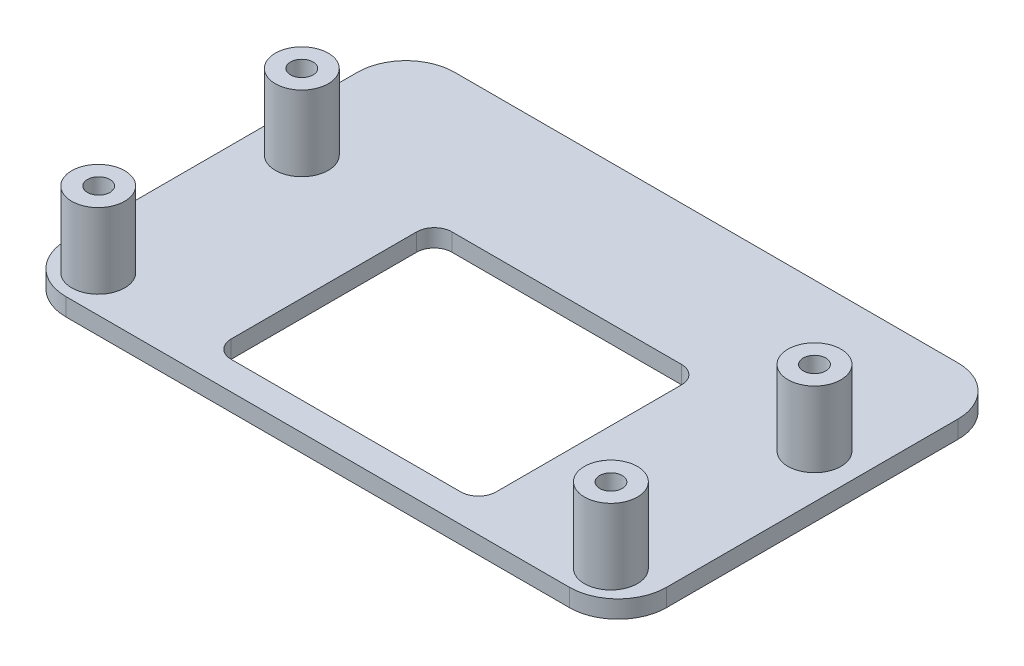
SolidWorks part; units mm, degrees
ref_plane "前视基准面" through (0, 0, 0) normal (0, 0, 1) x (1, 0, 0)
ref_plane "上视基准面" through (0, 0, 0) normal (0, 1, 0) x (1, 0, 0)
ref_plane "右视基准面" through (0, 0, 0) normal (1, 0, 0) x (0, 0, -1)
other "Configuration Table"
sketch "草图1" plane through (0, 0, 0) normal (0, 1, 0) x (1, 0, 0)
  line L1 (-34.4994, 19.3243) -> (33.5006, 19.3243)
  line L2 (-34.4994, 19.3243) -> (-34.4994, -24.6757)
  line L3 (-34.4994, -24.6757) -> (33.5006, -24.6757)
  line L4 (33.5006, 19.3243) -> (33.5006, -24.6757)
  dimension "D1" = 68
  dimension "D2" = 44
extrude "凸台-拉伸1" add sketch "草图1" along normal blind 2
fillet "圆角1" radius 5.5 4 edges at (33.5006, 1, -19.3243) (33.5006, 1, 24.6757) (-34.4994, 1, 24.6757) (-34.4994, 1, -19.3243)
sketch "草图2" plane through (0, 0, 0) normal (0, -1, 0) x (1, 0, 0)
  line L0 (-28.9994, 24.6757) -> (28.0006, 24.6757) construction
  line L1 (-15.4994, 21.4757) -> (14.5006, 21.4757)
  line L2 (-15.4994, 21.4757) -> (-15.4994, -3.5243)
  line L3 (-15.4994, -3.5243) -> (14.5006, -3.5243)
  line L4 (14.5006, 21.4757) -> (14.5006, -3.5243)
  line L5 (-15.4994, 21.4757) -> (14.5006, -3.5243) construction
  line L6 (-15.4994, -3.5243) -> (14.5006, 21.4757) construction
  point P0 (-0.4994, 8.9757)
  point P5 (0, 0)
  point P8 (-0.4994, 24.6757)
  dimension "D1" = 15.7
  dimension "D2" = 30
  dimension "D3" = 25
extrude "切除-拉伸1" cut sketch "草图2" against normal through all
fillet "圆角2" radius 2 4 edges at (-15.4994, 1, -3.5243) (-15.4994, 1, 21.4757) (14.5006, 1, 21.4757) (14.5006, 1, -3.5243)
sketch "草图3" plane through (0, 2, 0) normal (0, 1, 0) x (1, 0, 0)
  circle A0 centre (-29.5244, 2.5493) radius 3
  circle A1 centre (-29.5244, -20.5007) radius 3
  circle A2 centre (28.5006, -20.4757) radius 3
  circle A3 centre (28.5256, 2.5493) radius 3
  dimension "D1" = 6
extrude "凸台-拉伸2" add sketch "草图3" along normal blind 8.5
sketch "草图4" plane through (0, 10.5, 0) normal (0, 1, 0) x (1, 0, 0)
  circle A0 centre (-29.5244, 2.5493) radius 1.275
  circle A1 centre (-29.4994, -20.4757) radius 1.275
  circle A2 centre (28.5256, -20.5007) radius 1.275
  circle A3 centre (28.5256, 2.5493) radius 1.275
  dimension "D1" = 2.55
extrude "切除-拉伸2" cut sketch "草图4" against normal blind 6 draft 2
